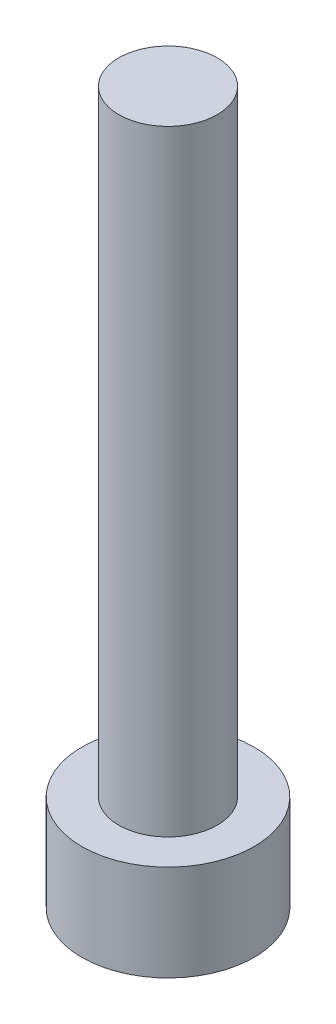
SolidWorks part; units mm, degrees
ref_plane "前视基准面" through (0, 0, 0) normal (0, 0, 1) x (1, 0, 0)
ref_plane "上视基准面" through (0, 0, 0) normal (0, 1, 0) x (1, 0, 0)
ref_plane "右视基准面" through (0, 0, 0) normal (1, 0, 0) x (0, 0, -1)
sketch "草图1" plane through (0, 0, 0) normal (0, 1, 0) x (1, 0, 0)
  circle A0 centre (0, 0) radius 3.5
extrude "凸台-拉伸1" add sketch "草图1" along normal blind 3.9
sketch "草图2" plane through (0, 3.9, 0) normal (0, 1, 0) x (1, 0, 0)
  circle A0 centre (0, 0) radius 2
extrude "凸台-拉伸2" add sketch "草图2" along normal blind 25
sketch "草图3" plane through (0, 0, 0) normal (0, -1, 0) x (1, 0, 0)
  line L1 (1.725, 0) -> (0.8625, 1.4939)
  line L2 (0.8625, 1.4939) -> (-0.8625, 1.4939)
  line L3 (-0.8625, 1.4939) -> (-1.725, 0)
  line L4 (-1.725, 0) -> (-0.8625, -1.4939)
  line L5 (-0.8625, -1.4939) -> (0.8625, -1.4939)
  line L6 (0.8625, -1.4939) -> (1.725, 0)
  circle A0 centre (0, 0) radius 1.4939 construction
extrude "切除-拉伸1" cut sketch "草图3" against normal blind 2.4
